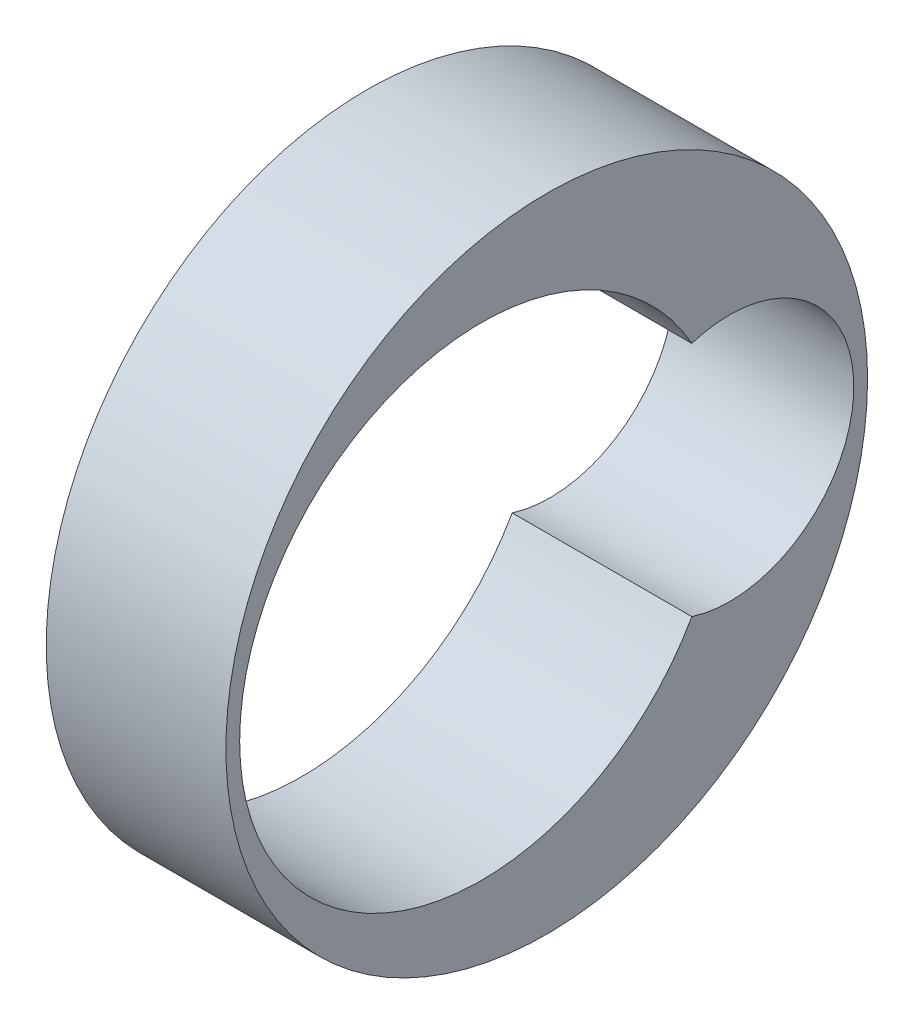
SolidWorks part; units mm, degrees
ref_plane "Front" through (0, 0, 0) normal (0, 0, 1) x (1, 0, 0)
ref_plane "Top" through (0, 0, 0) normal (0, 1, 0) x (1, 0, 0)
ref_plane "Right" through (0, 0, 0) normal (1, 0, 0) x (0, 0, -1)
sketch "Sketch1" plane through (0, 0, 0) normal (1, 0, 0) x (0, 0, -1)
  line L0 (23.6136, -0.5061) -> (8.7786, -0.5061) construction
  arc A0 (19.7009, 2.3517) -> (19.7009, -3.3639) centre (14.6136, -0.5061) ccw
  arc A1 (19.7009, -3.3639) -> (19.7009, 2.3517) centre (20.6136, -0.5061) ccw
  circle A2 centre (16.1961, -0.5061) radius 7.75
  point P9 (16.1961, -0.5061)
  dimension "D1" = 15.5
extrude "Boss-Extrude1" add sketch "Sketch1" along normal blind 4.34
